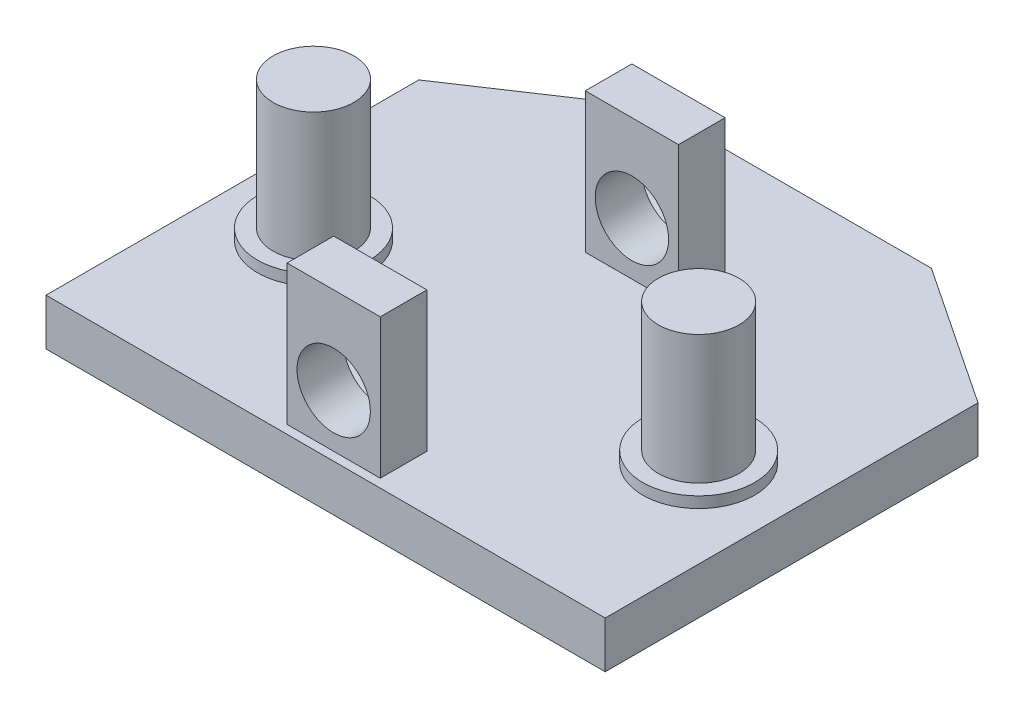
SolidWorks part; units mm, degrees
material "Acrylic (Medium-high impact)"
ref_plane "Front Plane" through (0, 0, 0) normal (0, 0, 1) x (1, 0, 0)
ref_plane "Top Plane" through (0, 0, 0) normal (0, 1, 0) x (1, 0, 0)
ref_plane "Right Plane" through (0, 0, 0) normal (1, 0, 0) x (0, 0, -1)
sketch "Sketch2" plane through (0, 0, 0) normal (0, 1, 0) x (1, 0, 0)
  line L0 (-38.1, 0) -> (38.1, 0)
  line L1 (-38.1, 0) -> (-38.1, 50.8)
  line L2 (38.1, 0) -> (38.1, 50.8)
  line L3 (0, 0) -> (0, 63.5) construction
  line L4 (-19.05, 63.5) -> (19.05, 63.5)
  line L7 (-38.1, 50.8) -> (-19.05, 63.5)
  line L8 (19.05, 63.5) -> (38.1, 50.8)
  point P4 (0, 0)
  point P12 (0, 63.5)
extrude "Boss-Extrude1" add sketch "Sketch2" along normal blind 6.35 contours L0 L2 L8 L4 L7 L1
sketch "Sketch3" plane through (0, 6.35, 0) normal (0, 1, 0) x (1, 0, 0)
  line L1 (-6.4223, 1.1712) -> (6.2777, 1.1712)
  line L2 (-6.4223, 1.1712) -> (-6.4223, 7.5212)
  line L3 (-6.4223, 7.5212) -> (6.2777, 7.5212)
  line L4 (6.2777, 1.1712) -> (6.2777, 7.5212)
  line L5 (-6.4223, 1.1712) -> (6.2777, 7.5212) construction
  line L6 (-6.4223, 7.5212) -> (6.2777, 1.1712) construction
  point P0 (-0.0723, 4.3462)
  point P5 (0, 7.6045)
  point P6 (0, 7.3119)
  point P7 (-0.0723, 4.3462)
extrude "Boss-Extrude2" add sketch "Sketch3" along normal blind 19.05
sketch "Sketch4" plane through (0, 0, -1.1712) normal (0, 0, 1) x (1, 0, 0)
  line L0 (-0.0723, 25.4) -> (-0.0723, 6.35) construction
  line L1 (-6.4223, 25.4) -> (6.2777, 25.4) construction
  line L2 (-6.4223, 6.35) -> (6.2777, 6.35) construction
  circle A0 centre (-0.0723, 13.5247) radius 5
  point P8 (0, 0)
  point P9 (-0.0723, 15.875)
  point P10 (-0.0723, 14.2424)
  point P11 (-0.0723, 13.5247)
extrude "Cut-Extrude1" cut sketch "Sketch4" against normal blind 12.7
pattern_linear "LPattern1" count 2 spacing 40.64 along (0, 0, -1) of "Boss-Extrude2", "Cut-Extrude1"
sketch "Sketch5" plane through (0, 6.35, 0) normal (0, 1, 0) x (1, 0, 0)
  line L0 (-0.0723, 7.5212) -> (-0.0723, 41.8112) construction
  line L1 (6.2777, 7.5212) -> (-6.4223, 7.5212) construction
  line L2 (-6.4223, 41.8112) -> (6.2777, 41.8112) construction
  line L3 (-26.3178, 24.6662) -> (26.1732, 24.6662) construction
  circle A0 centre (-26.3178, 24.6662) radius 5.5
  circle A1 centre (26.1732, 24.6662) radius 5.5
  point P9 (-0.0723, 24.6662)
extrude "Boss-Extrude3" add sketch "Sketch5" along normal blind 19.05
sketch "Sketch10" plane through (0, 6.35, 0) normal (0, 1, 0) x (1, 0, 0)
  line L0 (-0.0723, 41.8112) -> (-0.0723, 7.5212) construction
  line L1 (-6.4223, 41.8112) -> (6.2777, 41.8112) construction
  line L2 (6.2777, 7.5212) -> (-6.4223, 7.5212) construction
  line L3 (-26.3178, 24.6662) -> (26.1732, 24.6662) construction
  circle A0 centre (-26.3178, 24.6662) radius 7.62
  circle A1 centre (26.1732, 24.6662) radius 7.62
  point P9 (-0.0723, 24.6662)
extrude "Boss-Extrude4" add sketch "Sketch10" along normal blind 1.5
sketch "Sketch11" plane through (0, 25.4, 0) normal (0, 1, 0) x (1, 0, 0)
  line L0 (26.1732, 19.1662) -> (26.1732, 30.1662) construction
  circle A0 centre (26.1732, 24.6662) radius 5.5 construction
